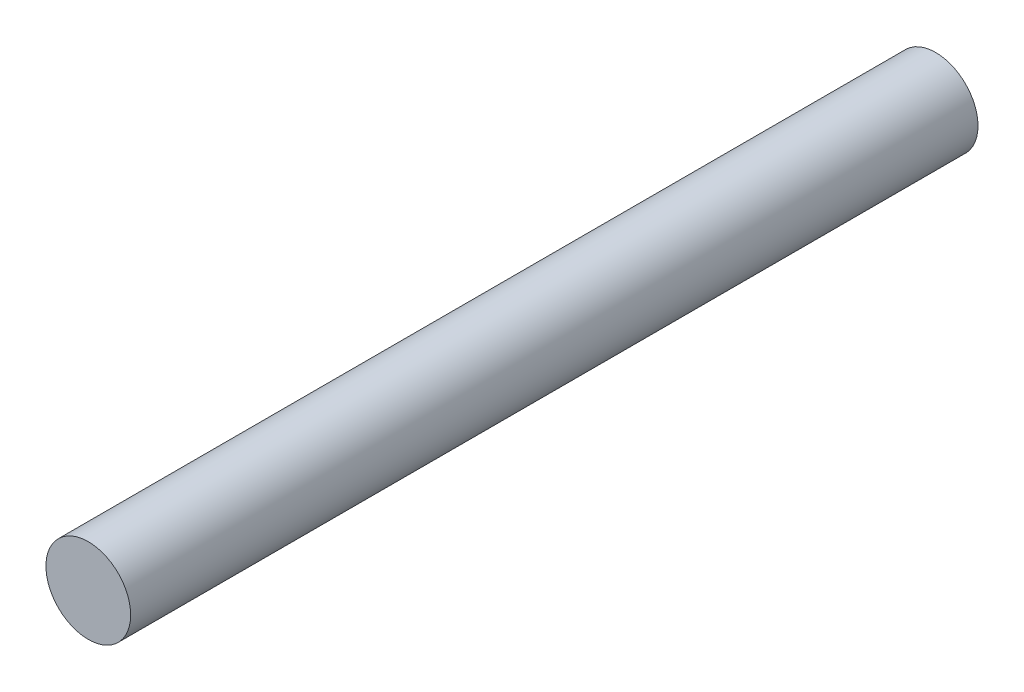
SolidWorks part; units mm, degrees
ref_plane "前视基准面" through (0, 0, 0) normal (0, 0, 1) x (1, 0, 0)
ref_plane "上视基准面" through (0, 0, 0) normal (0, 1, 0) x (1, 0, 0)
ref_plane "右视基准面" through (0, 0, 0) normal (1, 0, 0) x (0, 0, -1)
sketch "草图1" plane through (0, 0, 0) normal (0, 0, 1) x (1, 0, 0)
  circle A0 centre (0, 0) radius 3
  dimension "D1" = 6
extrude "凸台-拉伸1" add sketch "草图1" along normal blind 60
